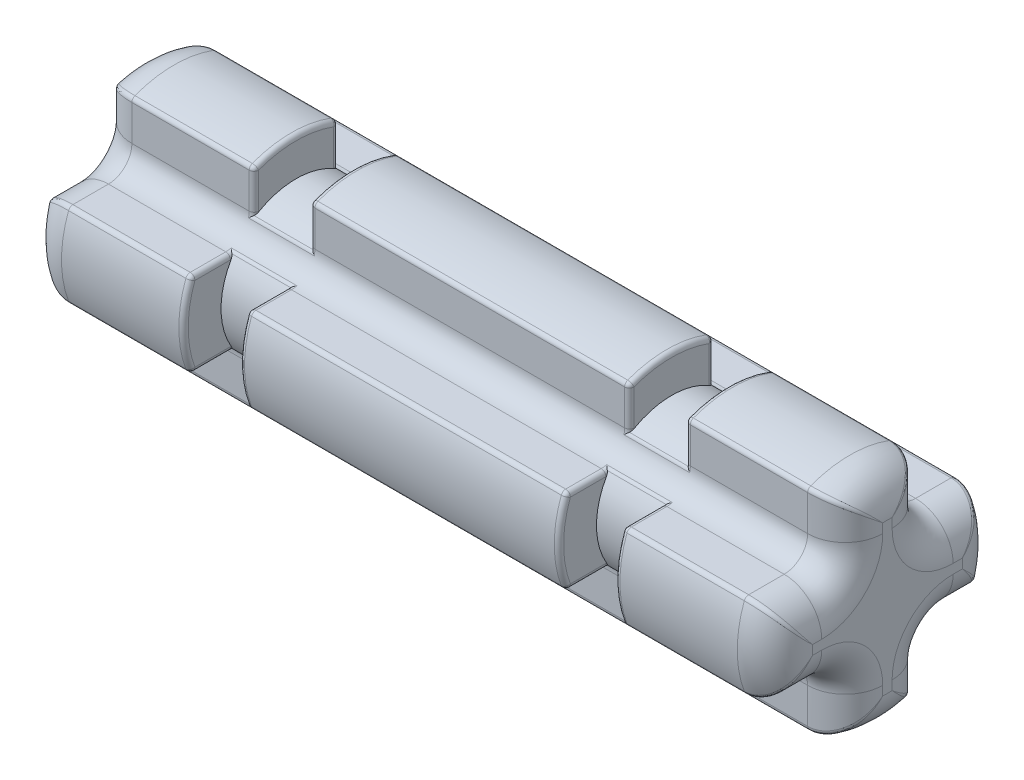
SolidWorks part; units mm, degrees
material "PET"
ref_plane "Alzado" through (0, 0, 0) normal (0, 0, 1) x (1, 0, 0)
ref_plane "Planta" through (0, 0, 0) normal (0, 1, 0) x (1, 0, 0)
ref_plane "Vista lateral" through (0, 0, 0) normal (1, 0, 0) x (0, 0, -1)
sketch "Croquis1" plane through (0, 0, 0) normal (1, 0, 0) x (0, 0, -1)
  line B0 (-1.4, 0.9) -> (-2.2249, 0.9)
  line B1 (0.9, -2.2249) -> (0.9, -1.4)
  line B2 (-0.9, -2.2249) -> (-0.9, -1.4)
  line B3 (2.2249, 0.9) -> (1.4, 0.9)
  line B4 (2.2249, -0.9) -> (1.4, -0.9)
  line B5 (-0.9, 1.4) -> (-0.9, 2.2249)
  line B6 (0.9, 1.4) -> (0.9, 2.2249)
  line B7 (-1.4, -0.9) -> (-2.2249, -0.9)
  arc B8 (-2.2249, 0.9) -> (-2.2249, -0.9) centre (0, 0) ccw
  arc B9 (-1.4, -0.9) -> (-0.9, -1.4) centre (-1.4, -1.4) cw
  arc B10 (0.9, -1.4) -> (1.4, -0.9) centre (1.4, -1.4) cw
  arc B11 (1.4, 0.9) -> (0.9, 1.4) centre (1.4, 1.4) cw
  arc B12 (-0.9, 1.4) -> (-1.4, 0.9) centre (-1.4, 1.4) cw
  arc B13 (0.9, 2.2249) -> (-0.9, 2.2249) centre (0, 0) ccw
  arc B14 (2.2249, -0.9) -> (2.2249, 0.9) centre (0, 0) ccw
  arc B15 (-0.9, -2.2249) -> (0.9, -2.2249) centre (0, 0) ccw
sketch_block_instance "Axle Section Block-1"
sketch_block "Axle Section Block" parameters "D1"=4.8, "D3"=0.5, "D2"=1.8
extrude "Saliente-Extruir1" add sketch "Croquis1" along normal blind 16
sketch "Croquis2" plane through (0, 0, 0) normal (0, 0, 1) x (1, 0, 0)
  line L0 (8, -0.9) -> (8, 0.9) construction
  line L1 (3.4, 1.6) -> (4.6, 1.6)
  line L2 (3.4, 1.6) -> (3.4, 3)
  line L3 (3.4, 3) -> (4.6, 3)
  line L4 (4.6, 1.6) -> (4.6, 3)
  line L5 (16, -0.9) -> (0, -0.9) construction
  line L6 (16, 0.9) -> (0, 0.9) construction
  line L7 (0, 0) -> (8, 0) construction
  line L8 (11.4, 1.6) -> (11.4, 3)
  line L9 (12.6, 3) -> (11.4, 3)
  line L10 (12.6, 1.6) -> (12.6, 3)
  line L11 (12.6, 1.6) -> (11.4, 1.6)
  line L12 (4, 1.6) -> (4, 3) construction
  line L13 (0, 0.9) -> (0, -0.9) construction
  dimension "D1" = 1.2
  dimension "D2" = 4
  dimension "D3" = 1.6
  dimension "D4" = 3
revolve "Cortar-Revolución1" cut sketch "Croquis2" angle 360 about L7
fillet "Redondeo2" radius 0.8 32 edges at (0, 1.8124, 0.9) (0, 1.0464, 1.0464) (0, 0.9, 1.8124) (0, 0, 2.4) (0, -0.9, 1.8124) (0, -1.0464, 1.0464) (0, -1.8124, 0.9) (0, -2.4, 0) (0, -1.8124, -0.9) (0, -1.0464, -1.0464) (0, -0.9, -1.8124) (0, 0, -2.4) (0, 0.9, -1.8124) (0, 1.0464, -1.0464) (0, 1.8124, -0.9) (0, 2.4, 0) (16, 1.8124, -0.9) (16, 1.0464, -1.0464) (16, 0.9, -1.8124) (16, 0, -2.4) (16, -0.9, -1.8124) (16, -1.0464, -1.0464) (16, -1.8124, -0.9) (16, -2.4, 0) (16, -1.8124, 0.9) (16, -1.0464, 1.0464) (16, -0.9, 1.8124) (16, 0, 2.4) (16, 0.9, 1.8124) (16, 1.0464, 1.0464) (16, 1.8124, 0.9) (16, 2.4, 0)
fillet "Redondeo1" radius 0.1 136 edges at (0.3666, 0.7725, -2.1371) (0.3666, -0.7725, -2.1371) (0.3666, -2.1371, -0.7725) (0.3666, -2.1371, 0.7725) (0.3666, -0.7725, 2.1371) (0.3666, 0.7725, 2.1371) (0.3666, 2.1371, 0.7725) (0.3666, 2.1371, -0.7725) (15.6334, 0.7725, -2.1371) (15.6334, -0.7725, -2.1371) (15.6334, -2.1371, -0.7725) (15.6334, -2.1371, 0.7725) (15.6334, -0.7725, 2.1371) (15.6334, 0.7725, 2.1371) (15.6334, 2.1371, -0.7725) (15.6334, 2.1371, 0.7725) (3.4, 1.8124, -0.9) (3.4, 0.9, -1.8124) (3.4, 0, -2.4) (2.1, 0.9, -2.2249) (3.4, -0.9, -1.8124) (2.1, -0.9, -2.2249) (3.4, -1.8124, -0.9) (3.4, -2.4, 0) (2.1, -2.2249, -0.9) (3.4, -1.8124, 0.9) (2.1, -2.2249, 0.9) (3.4, -0.9, 1.8124) (3.4, 0, 2.4) (2.1, -0.9, 2.2249) (3.4, 0.9, 1.8124) (2.1, 0.9, 2.2249) (3.4, 1.8124, 0.9) (3.4, 2.4, 0) (2.1, 2.2249, 0.9) (2.1, 2.2249, -0.9) (12.6, 1.8124, -0.9) (4.6, 1.8124, -0.9) (11.4, 1.8124, -0.9) (3.4, 0.9017, -1.359) (4, 1.3183, -0.9067) (4, 0.9067, -1.3183) (4.6, 0.9017, -1.359) (11.4, 0.9017, -1.359) (12, 1.3183, -0.9067) (12, 0.9067, -1.3183) (12.6, 0.9017, -1.359) (12.6, 1.359, -0.9017) (11.4, 1.359, -0.9017) (4.6, 1.359, -0.9017) (3.4, 1.359, -0.9017) (12.6, 0.9, -1.8124) (4.6, 0.9, -1.8124) (11.4, 0.9, -1.8124) (12.6, 0, -2.4) (13.9, 0.9, -2.2249) (8, 0.9, -2.2249) (4.6, 0, -2.4) (11.4, 0, -2.4) (12.6, -0.9, -1.8124) (13.9, -0.9, -2.2249) (8, -0.9, -2.2249) (4.6, -0.9, -1.8124) (11.4, -0.9, -1.8124) (3.4, -1.359, -0.9017) (4, -0.9067, -1.3183) (4, -1.3183, -0.9067) (4.6, -1.359, -0.9017) (11.4, -1.359, -0.9017) (12, -0.9067, -1.3183) (12, -1.3183, -0.9067) (12.6, -1.359, -0.9017) (12.6, -0.9017, -1.359) (11.4, -0.9017, -1.359) (4.6, -0.9017, -1.359) (3.4, -0.9017, -1.359) (12.6, -1.8124, -0.9) (4.6, -1.8124, -0.9) (11.4, -1.8124, -0.9) (12.6, -2.4, 0) (13.9, -2.2249, -0.9) (8, -2.2249, -0.9) (4.6, -2.4, 0) (11.4, -2.4, 0) (12.6, -1.8124, 0.9) (13.9, -2.2249, 0.9) (8, -2.2249, 0.9) (4.6, -1.8124, 0.9) (11.4, -1.8124, 0.9) (3.4, -0.9017, 1.359) (4, -1.3183, 0.9067) (4, -0.9067, 1.3183) (4.6, -0.9017, 1.359) (11.4, -0.9017, 1.359) (12, -1.3183, 0.9067) (12, -0.9067, 1.3183) (12.6, -0.9017, 1.359) (12.6, -1.359, 0.9017) (11.4, -1.359, 0.9017) (4.6, -1.359, 0.9017) (3.4, -1.359, 0.9017) (12.6, -0.9, 1.8124) (4.6, -0.9, 1.8124) (11.4, -0.9, 1.8124) (12.6, 0, 2.4) (13.9, -0.9, 2.2249) (8, -0.9, 2.2249) (4.6, 0, 2.4) (11.4, 0, 2.4) (12.6, 0.9, 1.8124) (13.9, 0.9, 2.2249) (8, 0.9, 2.2249) (4.6, 0.9, 1.8124) (11.4, 0.9, 1.8124) (3.4, 1.359, 0.9017) (4, 0.9067, 1.3183) (4, 1.3183, 0.9067) (4.6, 1.359, 0.9017) (11.4, 1.359, 0.9017) (12, 0.9067, 1.3183) (12, 1.3183, 0.9067) (12.6, 1.359, 0.9017) (12.6, 0.9017, 1.359) (11.4, 0.9017, 1.359) (4.6, 0.9017, 1.359) (3.4, 0.9017, 1.359) (12.6, 1.8124, 0.9) (4.6, 1.8124, 0.9) (11.4, 1.8124, 0.9) (12.6, 2.4, 0) (13.9, 2.2249, -0.9) (13.9, 2.2249, 0.9) (8, 2.2249, 0.9) (4.6, 2.4, 0) (8, 2.2249, -0.9) (11.4, 2.4, 0)
